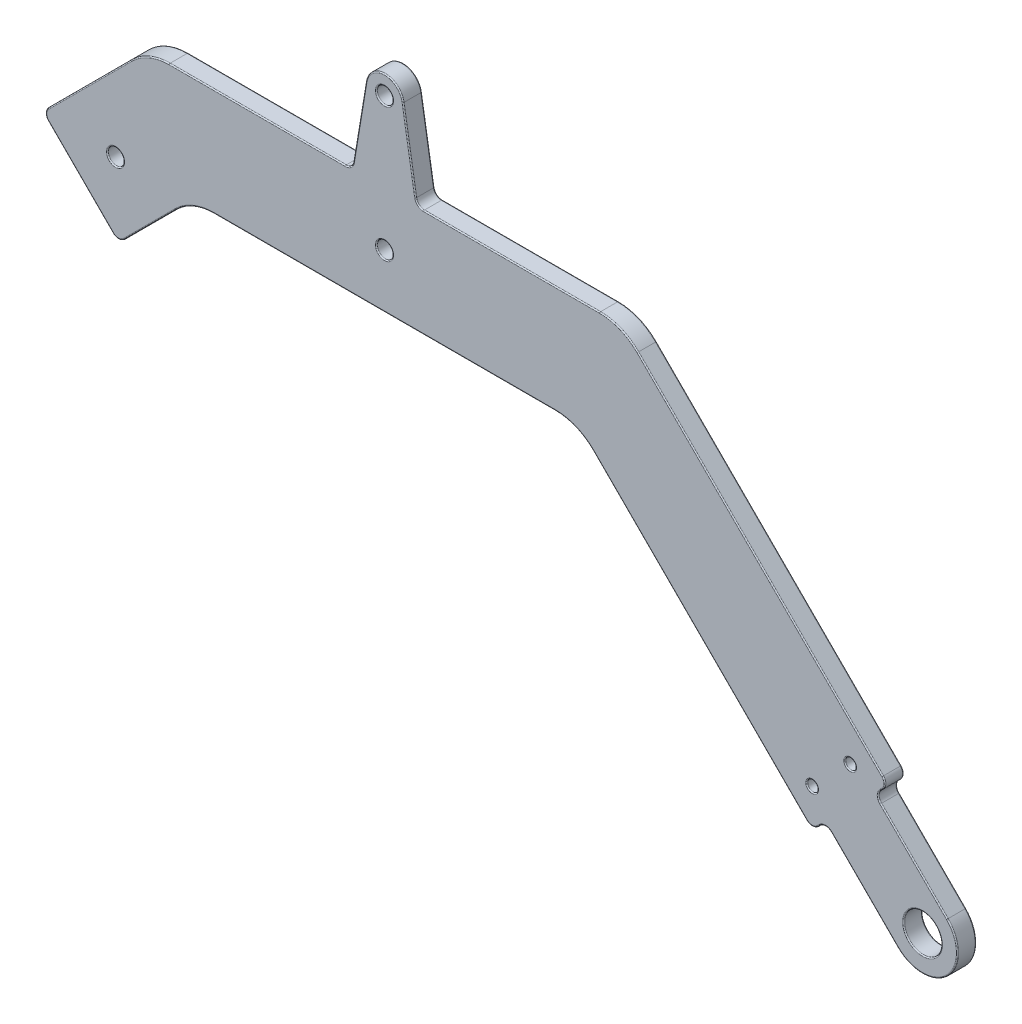
SolidWorks part; units mm, degrees
ref_plane "Front Plane" through (0, 0, 0) normal (0, 0, 1) x (1, 0, 0)
ref_plane "Top Plane" through (0, 0, 0) normal (0, 1, 0) x (1, 0, 0)
ref_plane "Right Plane" through (0, 0, 0) normal (1, 0, 0) x (0, 0, -1)
sketch "Sketch1" plane through (0, 0, 0) normal (0, 0, 1) x (1, 0, 0)
  line L0 (-100, 0) -> (100, 0) construction
  line L1 (-100, 0) -> (0, 100) construction
  line L2 (0, 100) -> (100, 0) construction
  line L3 (0, 100) -> (0, 60) construction
  line L4 (-40, 60) -> (40, 60) construction
  line L5 (0, 0) -> (-50, 50) construction
  circle A0 centre (-100, 0) radius 20
  circle A1 centre (0, 0) radius 20
  circle A2 centre (100, 0) radius 20
  point P4 (0, 0)
  point P9 (0, 60)
  dimension "D1" = 40
  dimension "D2" = 200
  dimension "D3" = 90
  dimension "D4" = 80
  dimension "D5" = 90
sketch "Sketch2" plane through (0, 0, 0) normal (0, 0, 1) x (1, 0, 0)
  line L0 (-56.5165, 43.4835) -> (-40, 60) construction
  line L1 (-100, 0) -> (0, 100) construction
  line L2 (-40, 60) -> (40, 60) construction
  line L3 (40, 60) -> (86.565, 13.435) construction
  line L4 (0, 100) -> (100, 0) construction
  line L5 (-49.4454, 36.4124) -> (-35.8579, 50)
  line L6 (-35.8579, 50) -> (35.8579, 50)
  line L7 (35.8579, 50) -> (79.4939, 6.364)
  line L8 (-63.5876, 50.5546) -> (-44.1421, 70)
  line L9 (-44.1421, 70) -> (44.1421, 70)
  line L10 (44.1421, 70) -> (93.636, 20.5061)
  line L11 (-63.5876, 50.5546) -> (-49.4454, 36.4124)
  line L12 (79.4939, 6.364) -> (93.636, 20.5061)
  line L13 (104.5962, 4.5962) -> (91.1612, 18.0312)
  line L14 (81.9688, 8.8388) -> (95.4038, -4.5962)
  line L15 (75.9584, 9.8995) -> (90.1005, 24.0416) construction
  line L16 (0, 100) -> (0, 60) construction
  line L17 (-3.4532, 85.4203) -> (-6, 70)
  line L18 (0, 84.85) -> (0, 84.8364) construction
  line L19 (3.4532, 85.4203) -> (6, 70)
  circle A0 centre (100, 0) radius 3.5
  circle A1 centre (100, 0) radius 10 construction
  arc A2 (95.4038, -4.5962) -> (104.5962, 4.5962) centre (100, 0) ccw
  circle A3 centre (79.4939, 13.435) radius 1
  circle A4 centre (100, 0) radius 6.5 construction
  circle A5 centre (86.565, 20.5061) radius 1
  circle A6 centre (0, 84.85) radius 1.5
  arc A7 (3.4532, 85.4203) -> (-3.4532, 85.4203) centre (0, 84.85) ccw
  circle A8 centre (0, 60) radius 1.5
  circle A9 centre (-50, 50) radius 1.5
  circle A10 centre (0, 84.85) radius 3.5 construction
  point P28 (106.5, 0)
  point P48 (3.5, 82)
  dimension "D4" = 7
  dimension "D5" = 20
  dimension "D9" = 2
  dimension "D11" = 14.85
  dimension "D12" = 3
  dimension "D14" = 6
  dimension "D15" = 3
  dimension "D1" = 10
  dimension "D3" = 27.5
  dimension "D7" = 19
  dimension "D8" = 5
  dimension "D10" = 5
  dimension "D2" = 10
  dimension "D6" = 3
  dimension "D13" = 2
sketch "Sketch3" plane through (0, 0, 0) normal (0, 0, 1) x (1, 0, 0)
  line L0 (-86.565, 13.435) -> (-50, 50) construction
  line L1 (-100, 0) -> (0, 100) construction
  line L2 (-50, 50) -> (-13.435, 13.435) construction
  line L3 (0, 0) -> (-50, 50) construction
  line L4 (-79.4939, 6.364) -> (-50, 35.8579)
  line L5 (-50, 35.8579) -> (-20.5061, 6.364)
  line L6 (-93.636, 20.5061) -> (-50, 64.1421)
  line L7 (-50, 64.1421) -> (-6.364, 20.5061)
  line L8 (-93.636, 20.5061) -> (-79.4939, 6.364)
  line L9 (-20.5061, 6.364) -> (-6.364, 20.5061)
  line L10 (-104.5962, 4.5962) -> (-91.1612, 18.0312)
  line L11 (-95.4038, -4.5962) -> (-81.9688, 8.8388)
  line L12 (-4.5962, -4.5962) -> (-18.0312, 8.8388)
  line L13 (4.534, 4.6576) -> (-9.0191, 17.8509)
  line L14 (-90.1005, 24.0416) -> (-75.9584, 9.8995) construction
  line L15 (-24.0416, 9.8995) -> (-9.8995, 24.0416) construction
  circle A0 centre (-100, 0) radius 3.5
  circle A1 centre (-100, 0) radius 10 construction
  circle A2 centre (0, 0) radius 3.5
  circle A3 centre (0, 0) radius 10 construction
  arc A4 (-4.5962, -4.5962) -> (4.534, 4.6576) centre (0, 0) ccw
  arc A5 (-104.5962, 4.5962) -> (-95.4038, -4.5962) centre (-100, 0) ccw
  circle A7 centre (0, 0) radius 20 construction
  circle A8 centre (-86.565, 20.5061) radius 1
  circle A9 centre (0, 0) radius 6.5 construction
  circle A10 centre (-79.4939, 13.435) radius 1
  circle A11 centre (-20.5061, 13.435) radius 1
  circle A12 centre (-13.435, 20.5061) radius 1
  circle A13 centre (-50, 50) radius 1.5 construction
  circle A14 centre (-50, 50) radius 1.5
  point P34 (6.5, 0)
  point P47 (0, 0)
  dimension "D1" = 7
  dimension "D2" = 20
  dimension "D4" = 10
  dimension "D10" = 2
  dimension "D6" = 19
  dimension "D7" = 19
  dimension "D8" = 5
  dimension "D9" = 5
  dimension "D11" = 5
  dimension "D12" = 5
  dimension "D3" = 3
  dimension "D5" = 10
sketch "Sketch4" plane through (0, 0, 0) normal (0, 0, 1) x (1, 0, 0)
  line L0 (0, 60) -> (0, 138.097) construction
  line L1 (-57.5, 93.3579) -> (57.5, 93.3579)
  line L2 (57.5, 93.3579) -> (57.5, 83.3579)
  line L3 (57.5, 83.3579) -> (44.1421, 70)
  line L4 (-44.1421, 70) -> (44.1421, 70) construction
  line L5 (44.1421, 70) -> (-44.1421, 70)
  line L6 (44.1421, 70) -> (93.636, 20.5061) construction
  line L7 (4, 60) -> (4, 70)
  line L8 (-4, 60) -> (-4, 70)
  line L9 (-57.5, 83.3579) -> (-44.1421, 70)
  line L10 (-57.5, 93.3579) -> (-57.5, 83.3579)
  line L11 (-22.5, 84.8579) -> (22.5, 84.8579) construction
  line L12 (-22.5, 89.3579) -> (22.5, 89.3579)
  line L13 (-22.5, 80.3579) -> (22.5, 80.3579)
  circle A0 centre (0, 60) radius 1.5 construction
  circle A1 centre (0, 60) radius 1.5
  arc A2 (-4, 60) -> (4, 60) centre (0, 60) ccw
  arc A3 (-22.5, 89.3579) -> (-22.5, 80.3579) centre (-22.5, 84.8579) ccw
  circle A4 centre (0, 60) radius 4 construction
  arc A5 (22.5, 80.3579) -> (22.5, 89.3579) centre (22.5, 84.8579) ccw
  point P23 (4, 60)
  point P25 (0, 70)
  point P27 (0, 93.3579)
  point P29 (0, 84.8579)
  point P30 (0, 0)
  point P35 (0, 0)
  dimension "D1" = 57.5
  dimension "D2" = 10
  dimension "D4" = 45
  dimension "D5" = 9
  dimension "D6" = 4
  dimension "D3" = 2.5
sketch "Sketch5" plane through (0, 0, 0) normal (0, 0, 1) x (1, 0, 0)
  line L0 (104.5962, 4.5962) -> (91.1612, 18.0312) construction
  line L1 (81.9688, 8.8388) -> (95.4038, -4.5962) construction
  line L2 (-3.4532, 85.4203) -> (-6, 70) construction
  line L3 (3.4532, 85.4203) -> (6, 70) construction
  line L4 (104.5962, 4.5962) -> (91.1612, 18.0312)
  line L5 (81.9688, 8.8388) -> (95.4038, -4.5962)
  line L6 (-3.4532, 85.4203) -> (-6, 70)
  line L7 (3.4532, 85.4203) -> (6, 70)
  line L8 (93.636, 20.5061) -> (44.1421, 70)
  line L9 (79.4939, 6.364) -> (93.636, 20.5061)
  line L10 (35.8579, 50) -> (79.4939, 6.364)
  line L11 (-35.8579, 50) -> (35.8579, 50)
  line L12 (-49.4454, 36.4124) -> (-35.8579, 50)
  line L13 (-63.5876, 50.5546) -> (-49.4454, 36.4124)
  line L14 (-44.1421, 70) -> (-63.5876, 50.5546)
  line L15 (44.1421, 70) -> (-44.1421, 70)
  line L16 (93.636, 20.5061) -> (44.1421, 70)
  line L17 (79.4939, 6.364) -> (81.9688, 8.8388)
  line L18 (35.8579, 50) -> (79.4939, 6.364)
  line L19 (-35.8579, 50) -> (35.8579, 50)
  line L20 (-49.4454, 36.4124) -> (-35.8579, 50)
  line L21 (-63.5876, 50.5546) -> (-49.4454, 36.4124)
  line L22 (-44.1421, 70) -> (-63.5876, 50.5546)
  line L23 (44.1421, 70) -> (6, 70)
  line L24 (-6, 70) -> (-44.1421, 70)
  line L25 (91.1612, 18.0312) -> (93.636, 20.5061)
  arc A0 (95.4038, -4.5962) -> (104.5962, 4.5962) centre (100, 0) ccw construction
  circle A1 centre (100, 0) radius 3.5
  circle A2 centre (100, 0) radius 3.5
  circle A3 centre (0, 60) radius 1.5
  circle A4 centre (0, 60) radius 1.5
  circle A5 centre (0, 84.85) radius 1.5
  circle A6 centre (0, 84.85) radius 1.5
  circle A7 centre (86.565, 20.5061) radius 1
  circle A8 centre (86.565, 20.5061) radius 1
  circle A9 centre (79.4939, 13.435) radius 1
  circle A10 centre (79.4939, 13.435) radius 1
  circle A11 centre (-50, 50) radius 1.5
  circle A12 centre (-50, 50) radius 1.5
  arc A13 (3.4532, 85.4203) -> (-3.4532, 85.4203) centre (0, 84.85) ccw construction
  arc A14 (95.4038, -4.5962) -> (104.5962, 4.5962) centre (100, 0) ccw
  arc A15 (3.4532, 85.4203) -> (-3.4532, 85.4203) centre (0, 84.85) ccw
  dimension "D1" = 0
  dimension "D2" = 0
  dimension "D3" = 0
  dimension "D4" = 0
  dimension "D5" = 0
  dimension "D6" = 0
  dimension "D7" = 0
extrude "Boss-Extrude1" add sketch "Sketch5" against normal blind 3.5
fillet "Fillet1" radius 10 4 edges at (-35.8579, 50, -1.75) (35.8579, 50, -1.75) (44.1421, 70, -1.75) (-44.1421, 70, -1.75)
fillet "Fillet2" radius 1.5 8 edges at (-49.4454, 36.4124, -1.75) (-63.5876, 50.5546, -1.75) (-6, 70, -1.75) (6, 70, -1.75) (93.636, 20.5061, -1.75) (91.1612, 18.0312, -1.75) (81.9688, 8.8388, -1.75) (79.4939, 6.364, -1.75)
fillet "Fillet3" radius 0.2 68 edges at (-35.5426, 49.2388, -3.5) (0, 50, -3.5) (35.5426, 49.2388, -3.5) (58.61, 27.2478, -3.5) (79.4939, 6.9853, -3.5) (80.7313, 7.6014, -3.5) (81.9688, 8.2175, -3.5) (89.2166, 1.591, -3.5) (104.5962, -4.5962, -3.5) (98.409, 10.7834, -3.5) (91.7825, 18.0312, -3.5) (92.3986, 19.2687, -3.5) (93.0147, 20.5061, -3.5) (69.8232, 44.3189, -3.5) (43.8268, 69.2388, -3.5) (23.6363, 70, -3.5) (6.3022, 70.3562, -3.5) (4.6229, 78.3379, -3.5) (0, 88.35, -3.5) (-4.6229, 78.3379, -3.5) (-6.3022, 70.3562, -3.5) (-23.6363, 70, -3.5) (-43.8268, 69.2388, -3.5) (-54.799, 59.3431, -3.5) (-62.9663, 50.5546, -3.5) (-56.5165, 43.4835, -3.5) (-49.4454, 37.0337, -3.5) (-43.5858, 42.2721, -3.5) (103.5, 0, -3.5) (1.5, 60, -3.5) (1.5, 84.85, -3.5) (87.565, 20.5061, -3.5) (80.4939, 13.435, -3.5) (-48.5, 50, -3.5) (-62.9663, 50.5546, 0) (-54.799, 59.3431, 0) (-43.8268, 69.2388, 0) (-23.6363, 70, 0) (-6.3022, 70.3562, 0) (-4.6229, 78.3379, 0) (0, 88.35, 0) (4.6229, 78.3379, 0) (6.3022, 70.3562, 0) (23.6363, 70, 0) (43.8268, 69.2388, 0) (69.8232, 44.3189, 0) (93.0147, 20.5061, 0) (92.3986, 19.2687, 0) (91.7825, 18.0312, 0) (98.409, 10.7834, 0) (104.5962, -4.5962, 0) (89.2166, 1.591, 0) (81.9688, 8.2175, 0) (80.7313, 7.6014, 0) (79.4939, 6.9853, 0) (58.61, 27.2478, 0) (35.5426, 49.2388, 0) (0, 50, 0) (-35.5426, 49.2388, 0) (-43.5858, 42.2721, 0) (-49.4454, 37.0337, 0) (-56.5165, 43.4835, 0) (103.5, 0, 0) (1.5, 60, 0) (1.5, 84.85, 0) (87.565, 20.5061, 0) (80.4939, 13.435, 0) (-48.5, 50, 0)
